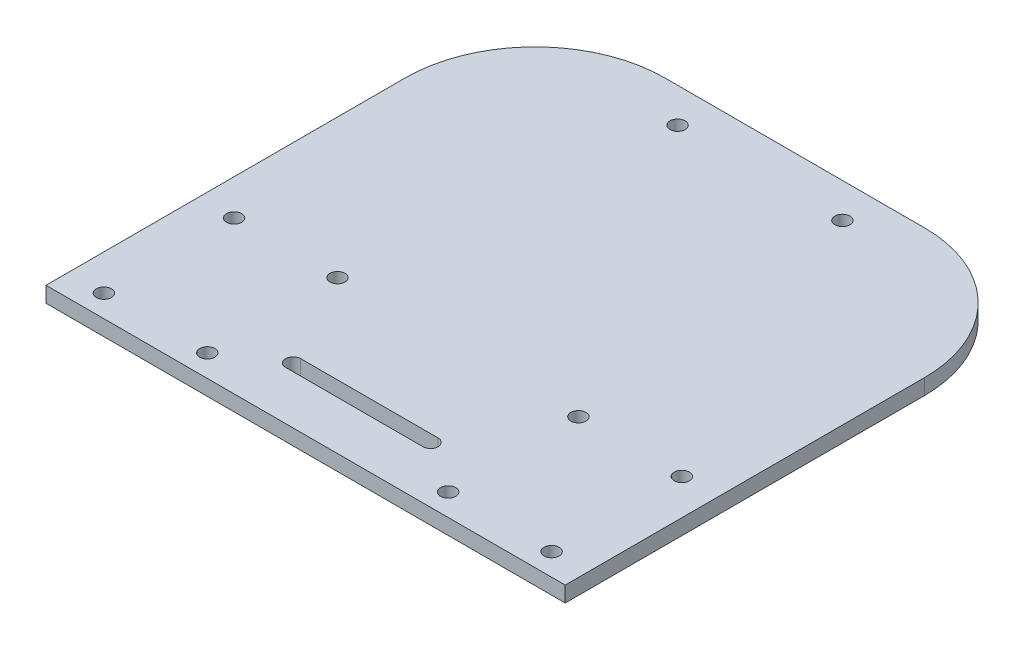
SolidWorks part; units mm, degrees
ref_plane "前视基准面" through (0, 0, 0) normal (0, 0, 1) x (1, 0, 0)
ref_plane "上视基准面" through (0, 0, 0) normal (0, 1, 0) x (1, 0, 0)
ref_plane "右视基准面" through (0, 0, 0) normal (1, 0, 0) x (0, 0, -1)
sketch "草图6" plane through (0, 0, 0) normal (0, 1, 0) x (1, 0, 0)
  line L0 (0, 0) -> (0, 140)
  line L1 (0, 0) -> (190, 0)
  line L2 (0, 140) -> (0, 0)
  line L3 (0, 140) -> (190, 140)
  line L4 (0, 0) -> (190, 0)
  line L5 (190, 140) -> (190, 0)
  line L6 (-905, 70) -> (49095, 70) construction
  line L7 (95, -930) -> (95, 49070) construction
  line L13 (-956.7369, 63.9433) -> (49043.2631, 63.9433) construction
  line L14 (35, 140) -> (155, 140)
  line L19 (35, 140) -> (35, 26.9827)
  line L20 (155, 140) -> (155, 26.9827)
  line L21 (35, 26.9827) -> (155, 26.9827)
  line L30 (95, 132) -> (63.2188, 132) construction
  line L31 (77.7, 132) -> (112.3, 132)
  line L32 (35.2131, 67.1433) -> (35.2131, 27.1433)
  line L33 (35.2131, 67.1433) -> (75.2131, 67.1433)
  line L34 (35.2131, 27.1433) -> (75.2131, 27.1433)
  line L35 (75.2131, 67.1433) -> (75.2131, 27.1433)
  line L36 (-964.7869, 47.1433) -> (49035.2131, 47.1433) construction
  line L37 (144.9869, -937.8067) -> (144.9869, 49062.1933) construction
  line L38 (134.7869, -932.8567) -> (134.7869, 49067.1433) construction
  line L39 (55.2131, -932.8567) -> (55.2131, 49067.1433) construction
  line L40 (45.0131, -937.8067) -> (45.0131, 49062.1933) construction
  line L41 (65.5131, -937.8067) -> (65.5131, 49062.1933) construction
  line L42 (69.0131, -937.8067) -> (69.0131, 49062.1933) construction
  line L43 (1146.7369, 63.9433) -> (-48853.2631, 63.9433) construction
  line L44 (120.9869, -937.8067) -> (120.9869, 49062.1933) construction
  line L45 (124.4869, -937.8067) -> (124.4869, 49062.1933) construction
  line L46 (1154.7869, 47.1433) -> (-48845.2131, 47.1433) construction
  line L47 (154.7869, 67.1433) -> (114.7869, 67.1433)
  line L48 (114.7869, 67.1433) -> (114.7869, 27.1433)
  line L49 (154.7869, 27.1433) -> (114.7869, 27.1433)
  line L50 (154.7869, 67.1433) -> (154.7869, 27.1433)
  line L51 (-909.5132, 39.9827) -> (49090.4868, 39.9827) construction
  line L52 (79.1225, 39.9827) -> (110.8775, 39.9827) construction
  line L53 (79.1225, 41.7327) -> (110.8775, 41.7327)
  line L54 (79.1225, 38.2327) -> (110.8775, 38.2327)
  line L55 (77.7, -868) -> (77.7, 49132) construction
  circle A8 centre (75.95, 132) radius 1.75
  circle A9 centre (114.05, 132) radius 1.75
  circle A10 centre (67.1631, 62.1933) radius 1.75
  circle A11 centre (43.2631, 62.1933) radius 1.75
  circle A12 centre (67.1631, 32.0933) radius 1.75
  circle A13 centre (43.2631, 32.0933) radius 1.75
  circle A14 centre (122.8369, 32.0933) radius 1.75
  circle A15 centre (146.7369, 32.0933) radius 1.75
  circle A16 centre (146.7369, 62.1933) radius 1.75
  circle A17 centre (122.8369, 62.1933) radius 1.75
  arc A18 (79.1225, 41.7327) -> (79.1225, 38.2327) centre (79.1225, 39.9827) ccw
  arc A19 (110.8775, 38.2327) -> (110.8775, 41.7327) centre (110.8775, 39.9827) ccw
  point P5 (95, 26.9827)
  point P12 (95, 70)
  point P17 (95, 70)
  point P21 (35.2131, 47.1433)
  point P28 (55.2131, 67.1433)
  point P56 (95, 132)
  point P79 (95, 39.9827)
  dimension "D1" = 0
  dimension "D3" = 20.5
  dimension "D5" = 140
  dimension "D7" = 8
  dimension "D9" = 3.2
  dimension "D10" = 3.5
  dimension "D11" = 40
  dimension "D13" = 0
  dimension "D15" = 3.5
  dimension "D2" = 120
  dimension "D4" = 6.2
  dimension "D6" = 190
  dimension "D8" = 34.6
  dimension "D12" = 13
extrude "凸台-拉伸2" add sketch "草图6" along normal blind 3.6
fillet "圆角1" radius 30 1 edges at (35, 1.8, -140)
fillet "圆角2" radius 30 1 edges at (155, 1.8, -140)
